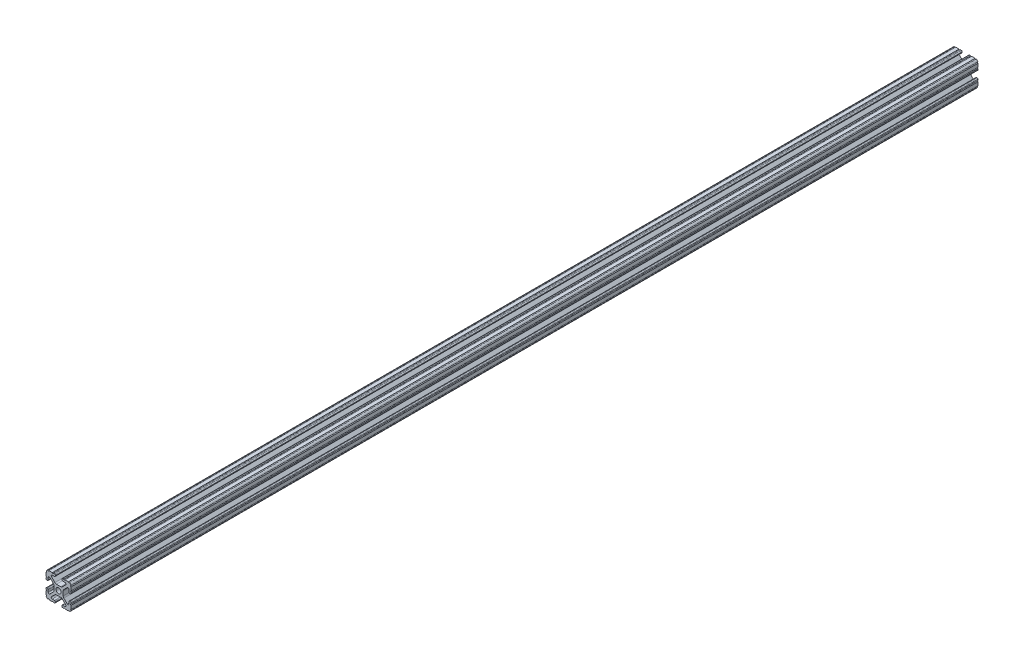
SolidWorks part; units mm, degrees
ref_plane "Front Plane" through (0, 0, 0) normal (0, 0, 1) x (1, 0, 0)
ref_plane "Top Plane" through (0, 0, 0) normal (0, 1, 0) x (1, 0, 0)
ref_plane "Right Plane" through (0, 0, 0) normal (1, 0, 0) x (0, 0, -1)
sketch "Sketch2" plane through (0, 0, 0) normal (0, 0, 1) x (1, 0, 0)
  line L0 (0, 12.7) -> (0, -12.7) construction
  line L1 (-12.7, 0) -> (12.7, 0) construction
  line L2 (3.2512, -12.7) -> (12.7, -12.7)
  line L3 (12.7, -12.7) -> (12.7, -3.2512)
  line L4 (3.2512, -12.7) -> (3.2512, -10.4902)
  line L5 (3.2512, -10.4902) -> (8.9276, -10.4902)
  line L6 (8.9276, -10.4902) -> (3.0856, -4.6482)
  line L7 (0, 0) -> (12.7, -12.7) construction
  line L8 (12.7, -3.2512) -> (10.4902, -3.2512)
  line L9 (10.4902, -3.2512) -> (10.4902, -8.9276)
  line L10 (10.4902, -8.9276) -> (4.6482, -3.0856)
  circle A0 centre (0, 0) radius 2.6035
  arc A1 (6.3485, -10.4902) -> (7.1039, -8.6665) centre (6.3485, -9.4219) ccw construction
  point P8 (0, -4.6482)
  dimension "Center Hole Diameter" = 5.207
  dimension "Rail Height" = 25.4
  dimension "Rail Width" = 25.4
  dimension "T-Slot Width" = 6.5024
  dimension "Slot Inner Width" = 14.8336
  dimension "Thickness" = 2.2098
  dimension "Slot Depth" = 5.842
  dimension "D1" = 2.2098
sketch "Sketch3" plane through (0, 0, 0) normal (1, 0, 0) x (0, 0, -1)
  line L0 (-457.2, -12.7) -> (457.2, -12.7) construction
  line L1 (-431.8, 0) -> (431.8, 0) construction
  dimension "Length" = 914.4
  dimension "D1" = 25.4
sketch "Sketch4" plane through (0, 0, 0) normal (0, 0, 1) x (1, 0, 0)
  line L0 (4.1904, -12.7) -> (10.1173, -12.7)
  line L1 (3.2512, -12.7) -> (12.7, -12.7) construction
  line L2 (3.2512, -12.7) -> (3.2512, -10.4902) construction
  line L3 (3.2512, -10.4902) -> (8.9276, -10.4902) construction
  line L4 (3.2512, -11.4294) -> (3.2512, -11.7608)
  line L5 (4.1904, -10.4902) -> (6.3485, -10.4902)
  line L6 (0, -4.6482) -> (2.164, -4.6482)
  line L7 (8.9276, -10.4902) -> (3.0856, -4.6482) construction
  line L8 (3.7373, -5.2999) -> (7.1039, -8.6665)
  line L9 (12.7, -12.7) -> (12.7, -3.2512) construction
  line L10 (10.4902, -8.9276) -> (4.6482, -3.0856) construction
  line L11 (10.4902, -3.2512) -> (10.4902, -8.9276) construction
  line L12 (10.4902, -6.3485) -> (10.4902, -4.1904)
  line L13 (12.7, -3.2512) -> (10.4902, -3.2512) construction
  line L14 (11.4294, -3.2512) -> (11.7608, -3.2512)
  line L15 (12.7, -4.1904) -> (12.7, -10.1173)
  line L16 (8.6665, -7.1039) -> (5.2999, -3.7373)
  line L17 (4.6482, 0) -> (4.6482, -2.164)
  line L18 (-12.7, 0) -> (12.7, 0) construction
  line L19 (0, -4.6482) -> (0, -2.6035)
  line L20 (0, 12.7) -> (0, -12.7) construction
  line L21 (4.6482, 0) -> (2.6035, 0)
  arc A0 (3.2512, -11.7608) -> (4.1904, -12.7) centre (4.1904, -11.7608) ccw
  arc A2 (3.2512, -11.4294) -> (4.1904, -10.4902) centre (4.1904, -11.4294) cw
  arc A3 (6.3485, -10.4902) -> (7.1039, -8.6665) centre (6.3485, -9.4219) ccw
  arc A4 (2.164, -4.6482) -> (3.7373, -5.2999) centre (2.164, -6.8732) cw
  arc A5 (10.1173, -12.7) -> (12.7, -10.1173) centre (10.1173, -10.1173) ccw
  arc A6 (8.6665, -7.1039) -> (10.4902, -6.3485) centre (9.4219, -6.3485) ccw
  arc A7 (10.4902, -4.1904) -> (11.4294, -3.2512) centre (11.4294, -4.1904) cw
  arc A8 (11.7608, -3.2512) -> (12.7, -4.1904) centre (11.7608, -4.1904) cw
  arc A9 (5.2999, -3.7373) -> (4.6482, -2.164) centre (6.8732, -2.164) cw
  circle A10 centre (0, 0) radius 2.6035 construction
  arc A11 (0, -2.6035) -> (2.6035, 0) centre (0, 0) ccw
  dimension "D1" = 2.5827
  dimension "D2" = 2.225
  dimension "D3" = 0.9392
extrude "Boss-Extrude1" add sketch "Sketch4" along normal mid plane 914.4
sketch "Sketch5" plane through (0, 0, 0) normal (0, 0, 1) x (1, 0, 0)
  line L0 (3.2512, -12.7) -> (12.7, -12.7) construction
  line L1 (4.1904, -10.4902) -> (6.3485, -10.4902) construction
  line L3 (0, 0) -> (12.7, -12.7) construction
  line L4 (6.3485, -10.4902) -> (6.3485, -12.7) construction
  line L5 (8.9276, -10.4902) -> (3.0856, -4.6482) construction
  circle A0 centre (10.3562, -12.7) radius 0.5524
  circle A1 centre (5.796, -12.7) radius 0.5524
  circle A2 centre (12.7, -10.3562) radius 0.5524
  circle A3 centre (12.7, -5.796) radius 0.5524
  point P10 (5.2694, -10.4902)
  point P12 (9.4219, -6.3485)
  dimension "D1" = 1.1049
extrude "Cut-Extrude1" cut sketch "Sketch5" against normal through all both and the other way through all
mirror "Mirror1" about plane through (0, 0, 0) normal (1, 0, 0) of bodies 137 134
mirror "Mirror2" about plane through (0, 0, 0) normal (0, 1, 0) of bodies 135
equation "\"D1@Boss-Extrude1\"=\"Length@Sketch3\""
equation "\"D1@Sketch2\"=\"Thickness@Sketch2\""
equation "\"D2@Sketch4\"=\"Slot Inner Width@Sketch2\"*0.15"
equation "\"D1@Sketch4\"=\"D3@Sketch4\"*2.75"
equation "\"D3@Sketch4\"=\"Thickness@Sketch2\"*0.425"
equation "\"D1@Sketch5\"=\"Thickness@Sketch2\"*0.5"
